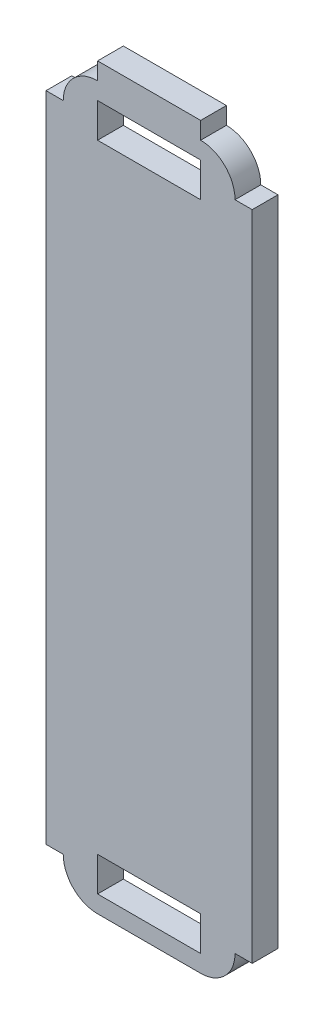
SolidWorks part; units mm, degrees
ref_plane "Płaszczyzna przednia" through (0, 0, 0) normal (0, 0, 1) x (1, 0, 0)
ref_plane "Płaszczyzna górna" through (0, 0, 0) normal (0, 1, 0) x (1, 0, 0)
ref_plane "Płaszczyzna prawa" through (0, 0, 0) normal (1, 0, 0) x (0, 0, -1)
sketch "Szkic1" plane through (0, 0, 0) normal (0, 0, 1) x (1, 0, 0)
  line L1 (0, 0) -> (10, 0)
  line L2 (0, 0) -> (0, 42)
  line L3 (0, 42) -> (10, 42)
  line L4 (10, 0) -> (10, 42)
  dimension "D1" = 10
  dimension "D2" = 42
extrude "Dodanie-wyciągnięcie1" add sketch "Szkic1" along normal blind 1.5
fillet "Zaokrąglenie1" radius 2 4 edges at (10, 0, 0.75) (0, 0, 0.75) (10, 42, 0.75) (0, 42, 0.75)
sketch "Szkic2" plane through (10, 0, 0) normal (1, 0, 0) x (0, 0, -1)
  line L1 (-1.5, 40) -> (0, 40)
  line L2 (-1.5, 40) -> (-1.5, 2)
  line L3 (-1.5, 2) -> (0, 2)
  line L4 (0, 40) -> (0, 2)
extrude "Dodanie-wyciągnięcie2" add sketch "Szkic2" along normal blind 1
sketch "Szkic3" plane through (0, 0, 0) normal (-1, 0, 0) x (0, 0, 1)
  line L1 (0, 40) -> (1.5, 40)
  line L2 (0, 40) -> (0, 2)
  line L3 (0, 2) -> (1.5, 2)
  line L4 (1.5, 40) -> (1.5, 2)
extrude "Dodanie-wyciągnięcie3" add sketch "Szkic3" along normal blind 1
sketch "Szkic4" plane through (0, 42, 0) normal (0, 1, 0) x (1, 0, 0)
  line L1 (2, 0) -> (8, 0)
  line L2 (2, 0) -> (2, -1.5)
  line L3 (2, -1.5) -> (8, -1.5)
  line L4 (8, 0) -> (8, -1.5)
extrude "Dodanie-wyciągnięcie4" add sketch "Szkic4" along normal blind 1
sketch "Szkic5" plane through (0, 0, 0) normal (0, 0, -1) x (-1, 0, 0)
  line L0 (-2, 0) -> (-8, 0) construction
  line L1 (-8, 43) -> (-2, 43) construction
  line L2 (-8, 41) -> (-2, 41)
  line L3 (-8, 41) -> (-8, 39)
  line L4 (-8, 39) -> (-2, 39)
  line L5 (-2, 41) -> (-2, 39)
  line L6 (-2, 1) -> (-8, 1)
  line L7 (-2, 1) -> (-2, 3)
  line L8 (-2, 3) -> (-8, 3)
  line L9 (-8, 1) -> (-8, 3)
  point P4 (-5, 0)
  point P8 (-8, 2)
  point P12 (-2, 40)
  point P18 (-5, 43)
  point P19 (-5, 41)
  point P20 (-5, 3)
  dimension "D2" = 2
  dimension "D4" = 2
  dimension "D1" = 2
  dimension "D3" = 6
extrude "Wytnij-wyciągnięcie2" cut sketch "Szkic5" against normal through all
